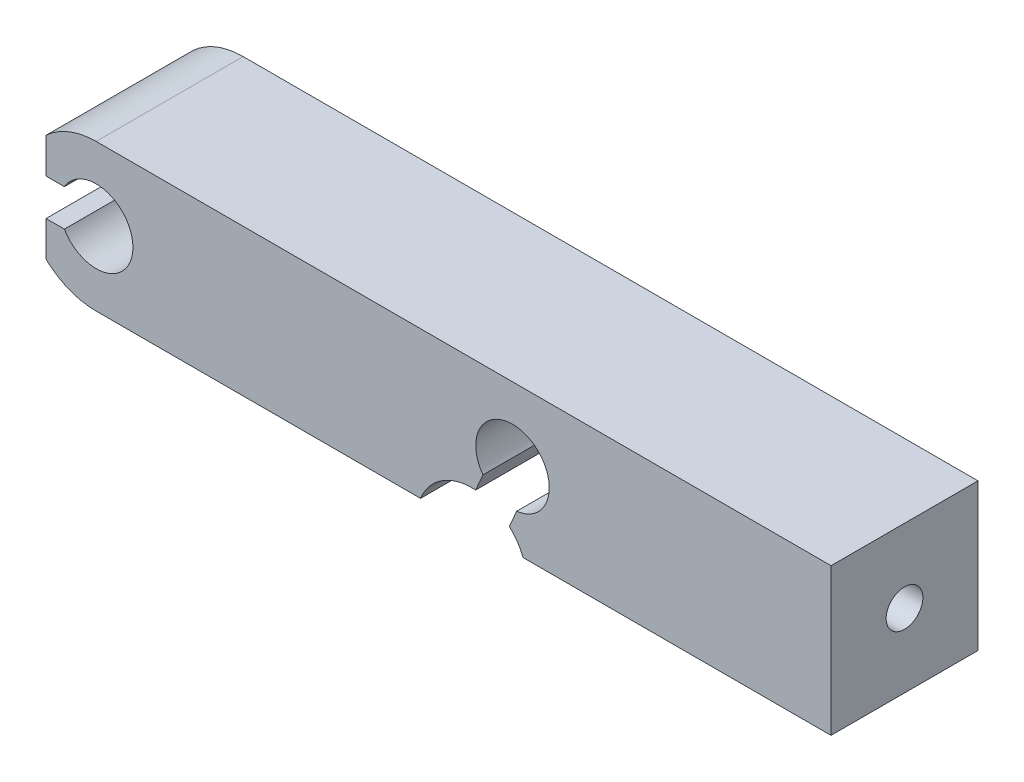
SolidWorks part; units mm, degrees
ref_plane "前视基准面" through (0, 0, 0) normal (0, 0, 1) x (1, 0, 0)
ref_plane "上视基准面" through (0, 0, 0) normal (0, 1, 0) x (1, 0, 0)
ref_plane "右视基准面" through (0, 0, 0) normal (1, 0, 0) x (0, 0, -1)
sketch "草图3" plane through (0, 0, 0) normal (0, 0, 1) x (1, 0, 0)
  line L0 (-1000, 0) -> (49000, 0) construction
  line L1 (20, -2) -> (20, 2)
  line L2 (20, 2) -> (0, 2)
  line L3 (20, -2) -> (0, -2)
  circle A0 centre (0, 0) radius 2
  point P11 (20, 0)
  dimension "D1" = 4
  dimension "D2" = 2
  dimension "D3" = 20
extrude "凸台-拉伸1" add sketch "草图3" along normal blind 4 contours L0 A0 | A0 L0 | A0 L0 L1 L2 | L0 A0 L3 L1
sketch "草图4" plane through (20, 0, 0) normal (1, 0, 0) x (0, 0, -1)
  line L0 (-1004, 0) -> (48996, 0) construction
  line L1 (-4, -2) -> (-4, 2) construction
  line L2 (-2, -998) -> (-2, 49002) construction
  line L3 (-4, 2) -> (0, 2) construction
  circle A0 centre (-2, 0) radius 0.5
  point P5 (-4, 0)
  point P10 (-2, 2)
  dimension "D1" = 1
extrude "切除-拉伸1" cut sketch "草图4" against normal blind 7
sketch "草图5" plane through (0, 0, 4) normal (0, 0, 1) x (1, 0, 0)
  line L0 (-1000, 0) -> (49000, 0) construction
  line L1 (-0.866, 0.5) -> (-1.366, 0.5)
  line L2 (-0.866, -0.5) -> (-1.366, -0.5)
  line L4 (-1.366, 0.5) -> (-1.366, 1.4608)
  line L5 (-1.366, -0.5) -> (-1.366, -1.4608)
  arc A0 (-0.866, -0.5) -> (-0.866, 0.5) centre (0, 0) ccw
  arc A1 (0, 2) -> (0, -2) centre (0, 0) ccw construction
  arc A2 (-1.9365, 0.5) -> (-1.9365, -0.5) centre (0, 0) ccw
  arc A3 (-1.366, 1.4608) -> (-1.366, -1.4608) centre (0, 0) ccw
  dimension "D1" = 2
  dimension "D2" = 1
extrude "切除-拉伸4" cut sketch "草图5" against normal blind 3 contours L4 L0 A0 L1 | L0 A3 L4 L5 L2 A0
sketch "草图6" plane through (0, 0, 1) normal (0, 0, 1) x (1, 0, 0)
  line L0 (-1.366, 0.5) -> (-1.366, -0.5)
  line L4 (-1.366, -1.4608) -> (-1.366, -0.5)
  line L5 (-1.366, -0.5) -> (-0.866, -0.5)
  line L6 (-0.866, 0.5) -> (-1.366, 0.5)
  line L7 (-1.366, 0.5) -> (-1.366, 1.4608)
  line L8 (-1.366, -1.4608) -> (-1.366, -0.5)
  line L11 (-1.366, 0.5) -> (-1.366, 1.4608)
  arc A2 (-1.366, 1.4608) -> (-1.366, -1.4608) centre (0, 0) ccw
  arc A3 (-0.866, -0.5) -> (-0.866, 0.5) centre (0, 0) ccw
  arc A4 (-1.366, 1.4608) -> (-1.366, -1.4608) centre (0, 0) ccw
  dimension "D1" = 0
extrude "切除-拉伸5" cut sketch "草图6" against normal blind 3
sketch "草图7" plane through (0, 0, 4) normal (0, 0, 1) x (1, 0, 0)
  line L0 (0, 0) -> (11.3308, 0) construction
  line L1 (11.3308, 0) -> (10.0057, -3.0524) construction
  line L2 (20, -2) -> (0, -2) construction
  line L3 (10.5273, -0.5953) -> (10.3282, -1.054)
  line L4 (11.4446, -0.9935) -> (11.2455, -1.4522)
  line L5 (10.6845, -2) -> (11.5535, -2) construction
  line L6 (9.9175, -2) -> (11.0076, -2)
  line L8 (9.9175, -2) -> (8.8283, -2)
  line L9 (11.0076, -2) -> (11.6191, -2)
  arc A0 (11.4446, -0.9935) -> (10.5273, -0.5953) centre (11.3308, 0) ccw
  arc A1 (11.6191, -2) -> (11.2455, -1.4522) centre (10.2237, -2.5503) ccw
  arc A2 (10.3282, -1.054) -> (8.8283, -2) centre (10.2237, -2.5503) ccw
  dimension "D2" = 2
  dimension "D6" = 3
  dimension "D1" = 11.3308
  dimension "D3" = 66.535
  dimension "D4" = 0.5
extrude "切除-拉伸6" cut sketch "草图7" against normal blind 3
